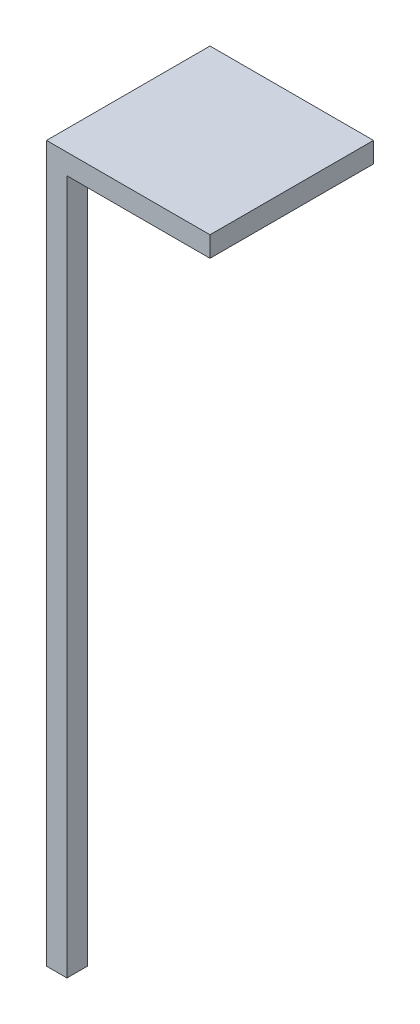
SolidWorks part; units mm, degrees
ref_plane "Face" through (0, 0, 0) normal (0, 0, 1) x (1, 0, 0)
ref_plane "Dessus" through (0, 0, 0) normal (0, 1, 0) x (1, 0, 0)
ref_plane "Droite" through (0, 0, 0) normal (1, 0, 0) x (0, 0, -1)
sketch "Esquisse1" plane through (0, 0, 0) normal (0, 1, 0) x (1, 0, 0)
  line L1 (0, 0) -> (10, 0)
  line L2 (0, 0) -> (0, 10)
  line L3 (0, 10) -> (10, 10)
  line L4 (10, 0) -> (10, 10)
  dimension "D1" = 10
  dimension "D2" = 10
extrude "Extrusion1" add sketch "Esquisse1" along normal blind 340
sketch "Esquisse2" plane through (0, 340, 0) normal (0, 1, 0) x (1, 0, 0)
  line L1 (0, 0) -> (80, 0)
  line L2 (0, 0) -> (0, 80)
  line L3 (0, 80) -> (80, 80)
  line L4 (80, 0) -> (80, 80)
  dimension "D1" = 80
  dimension "D2" = 80
extrude "Extrusion2" add sketch "Esquisse2" along normal blind 10
